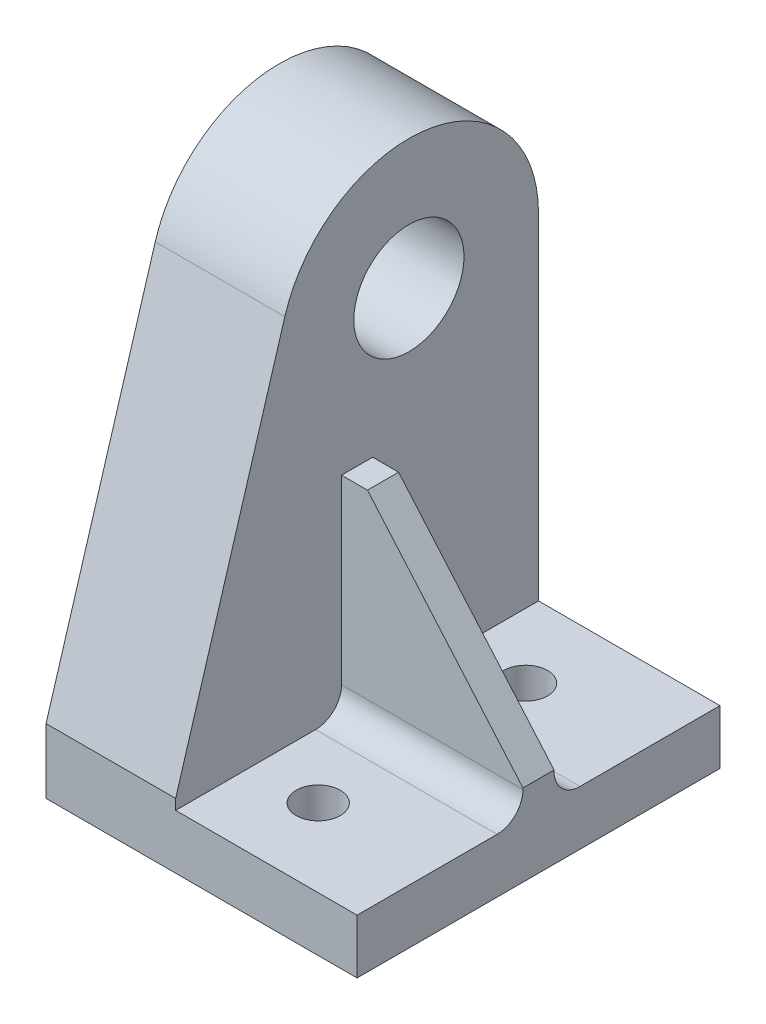
SolidWorks part; units mm, degrees
material "ABS"
ref_plane "Front" through (0, 0, 0) normal (0, 0, 1) x (1, 0, 0)
ref_plane "Top" through (0, 0, 0) normal (0, 1, 0) x (1, 0, 0)
ref_plane "Right" through (0, 0, 0) normal (1, 0, 0) x (0, 0, -1)
sketch "Croquis1" plane through (0, 0, 0) normal (0, 0, 1) x (1, 0, 0)
  line L0 (0, 4.2) -> (-14, 4.2)
  line L1 (-14, 4.2) -> (-14, 40.1)
  line L2 (-14, 40.1) -> (-24, 40.1)
  line L3 (-24, 40.1) -> (-24, 0)
  line L4 (-24, 0) -> (0, 0)
  line L5 (0, 4.2) -> (0, 9.8876) construction
  line L6 (0, 4.2) -> (0, 0)
  dimension "D1" = 40.1
  dimension "D2" = 4.2
  dimension "D3" = 10
  dimension "D4" = 14
extrude "Saliente-Extruir1" add sketch "Croquis1" along normal blind 28
sketch "Croquis2" plane through (-24, 0, 0) normal (-1, 0, 0) x (0, 0, 1)
  line L0 (28, 5) -> (19.5755, 32.9828)
  line L1 (0, 40.1) -> (0, 0) construction
  line L2 (28, 40.1) -> (0, 40.1) construction
  line L3 (0, 30.1) -> (0, 29.1)
  line L4 (0, 29.1) -> (-1, 29.1)
  line L5 (-1, 29.1) -> (-1, 41.1)
  line L6 (-1, 41.1) -> (29, 41.1)
  line L7 (28, 5) -> (29, 5)
  line L8 (29, 5) -> (29, 41.1)
  line L9 (28, 40.1) -> (28, 0) construction
  line L10 (28, 0) -> (0, 0) construction
  arc A0 (19.5755, 32.9828) -> (0, 30.1) centre (10, 30.1) ccw
  circle A1 centre (10, 30.1) radius 4.25
  dimension "D4" = 8.5
  dimension "D5" = 10
  dimension "D1" = 1
  dimension "D2" = 1
  dimension "D3" = 1
  dimension "D6" = 5
extrude "Cortar-Extruir1" cut sketch "Croquis2" against normal through all
sketch "Croquis3" plane through (0, 0, 0) normal (0, -1, 0) x (1, 0, 0)
  line L0 (0, 28) -> (0, 0) construction
  line L1 (9, 6) -> (-9, 6) construction
  line L2 (9, 6) -> (9, 22) construction
  line L3 (9, 22) -> (-9, 22) construction
  line L4 (-9, 6) -> (-9, 22) construction
  line L5 (9, 6) -> (-9, 22) construction
  line L6 (9, 22) -> (-9, 6) construction
  circle A0 centre (-9, 22) radius 1.7
  circle A1 centre (-9, 6) radius 1.7
  point P0 (0, 14)
  dimension "D1" = 3.4
  dimension "D2" = 16
  dimension "D3" = 18
extrude "Cortar-Extruir2" cut sketch "Croquis3" against normal up to next
ref_plane "Plano1" through (0, 0, 14) normal (0, 0, -1) x (-1, 0, 0)
sketch "Croquis4" plane through (0, 0, 14) normal (0, 0, -1) x (-1, 0, 0)
  line L0 (0, 4.2) -> (14, 4.2)
  line L1 (14, 4.2) -> (14, 20.2)
  line L2 (14, 4.2) -> (14, 30.1) construction
  line L3 (14, 20.2) -> (12, 20.2)
  line L4 (12, 20.2) -> (0, 6.3)
  line L5 (0, 4.2) -> (0, 6.3)
  dimension "D1" = 2.1
  dimension "D2" = 2
  dimension "D3" = 16
extrude "Saliente-Extruir2" add sketch "Croquis4" along normal mid plane 2.4
fillet "Redondeo1" radius 2 2 edges at (-7, 4.2, 12.8) (-7, 4.2, 15.2)
